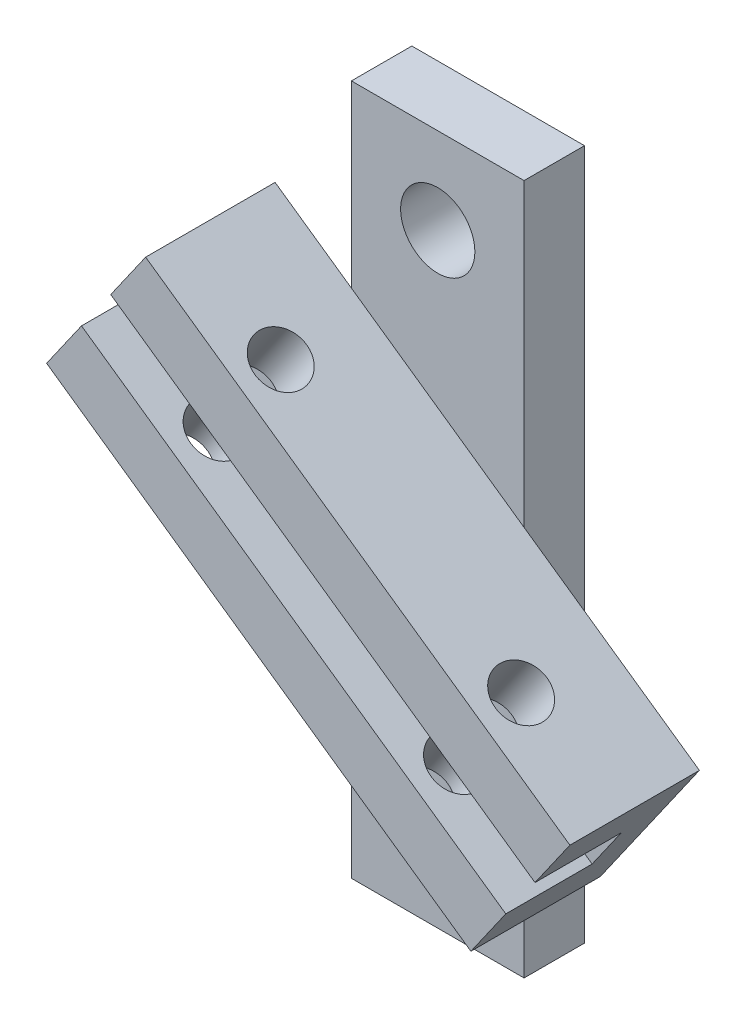
SolidWorks part; units mm, degrees
ref_plane "Ebene vorne" through (0, 0, 0) normal (0, 0, 1) x (1, 0, 0)
ref_plane "Ebene oben" through (0, 0, 0) normal (0, 1, 0) x (1, 0, 0)
ref_plane "Ebene rechts" through (0, 0, 0) normal (1, 0, 0) x (0, 0, -1)
sketch "Skizze1" plane through (0, 0, 0) normal (0, 0, 1) x (1, 0, 0)
  line L0 (10, 80) -> (10, 0) construction
  line L1 (0, 0) -> (20, 0)
  line L2 (0, 0) -> (0, 80)
  line L3 (0, 80) -> (20, 80)
  line L4 (20, 0) -> (20, 80)
  line L5 (0, 70) -> (20, 70) construction
  line L6 (0, 40) -> (20, 40) construction
  circle A0 centre (10, 70) radius 4.3
  circle A1 centre (10, 10) radius 4.3
  dimension "D4" = 8.6
  dimension "D1" = 80
  dimension "D2" = 20
  dimension "D3" = 10
extrude "Aufsatz-Linear austragen1" add sketch "Skizze1" along normal blind 7
sketch "Skizze2" plane through (0, 0, 7) normal (0, 0, 1) x (1, 0, 0)
  line L0 (-8.8388, 65.3988) -> (-20.3103, 49.0158)
  line L1 (-20.3103, 49.0158) -> (28.8388, 14.6012)
  line L2 (28.8388, 14.6012) -> (40.3103, 30.9842)
  line L3 (40.3103, 30.9842) -> (-8.8388, 65.3988)
  line L4 (0, 80) -> (20, 80)
  line L5 (15.7358, 48.1915) -> (4.2642, 31.8085) construction
  line L6 (0, 0) -> (20, 0)
  line L7 (10, 0) -> (10, 80) construction
  line L8 (-12.8825, 59.6238) -> (36.2666, 25.2092)
  line L9 (-16.2666, 54.7908) -> (32.8825, 20.3762)
  line L10 (-14.5746, 57.2073) -> (34.5746, 22.7927) construction
  point P17 (10, 40)
  line M6 (0, 80) -> (0, 0)
  line M8 (20, 0) -> (20, 80)
  dimension "D1" = 20
  dimension "D2" = 60
  dimension "D3" = 325
  dimension "D4" = 5.9
  dimension "D5" = 40
extrude "Aufsatz-Linear austragen2" add sketch "Skizze2" along normal blind 15 contours L9 L1 L2 M8 | L9 L2 L8 M8 | L8 L2 L3 M8 | L8 L3 M6 M8 | L9 L8 M6 M8 | L9 L1 M6 M8 | L9 L0 L1 M6 | L0 L9 L8 M6 | L0 L8 L3 M6
sketch "Skizze3" plane through (0, 0, 22) normal (0, 0, 1) x (1, 0, 0)
  line L0 (-16.2666, 54.7908) -> (32.8825, 20.3762)
  line L1 (32.8825, 20.3762) -> (36.2666, 25.2092)
  line L2 (36.2666, 25.2092) -> (-12.8825, 59.6238)
  line L4 (-12.8825, 59.6238) -> (-16.2666, 54.7908)
extrude "Schnitt-Linear austragen1" cut sketch "Skizze3" against normal blind 10
sketch "Skizze5" plane through (27.8195, 39.7304, 0) normal (0.5736, 0.8192, 0) x (0.8192, -0.5736, 0)
  line L0 (-44.7515, -17) -> (15.2485, -17) construction
  line L1 (-44.7515, -7) -> (15.2485, -7)
  line L2 (-44.7515, -7) -> (-44.7515, -22)
  line L3 (-44.7515, -22) -> (15.2485, -22)
  line L4 (15.2485, -7) -> (15.2485, -22)
  line L5 (2.2485, -7) -> (2.2485, -22) construction
  line L6 (-14.7515, -7) -> (-14.7515, -22) construction
  circle A0 centre (2.2485, -17) radius 3
  circle A1 centre (-31.7515, -17) radius 3
  dimension "D1" = 6
  dimension "D2" = 13
  dimension "D3" = 5
hole_wizard "Ø6.0 (6) Durchmesser Bohrung1" positions "Skizze6" profile "Skizze7" hole size "Ø6.0" standard "DIN" end condition through all
sketch "Skizze6" plane through (27.8195, 39.7304, 0) normal (0.5736, 0.8192, 0) x (0.8192, -0.5736, 0)
  point P0 (2.2485, -17)
  point P3 (-31.7515, -17)
sketch "Skizze7" plane through (29.6613, 38.4407, 17) normal (0, 0, 1) x (-0.8192, 0.5736, 0)
  line L0 (0, 0) -> (0, 60.1514)
  line L1 (0, 60.1514) -> (3, 60.1514)
  line L2 (3, 60.1514) -> (3, 0)
  line L5 (3, 0) -> (0, 0)
  line L11 (0, -6.35) -> (0, 107.95) construction
  dimension "Bohrerdurchmesser" = 6
  dimension "Bohrungstiefe" = 60.1514
